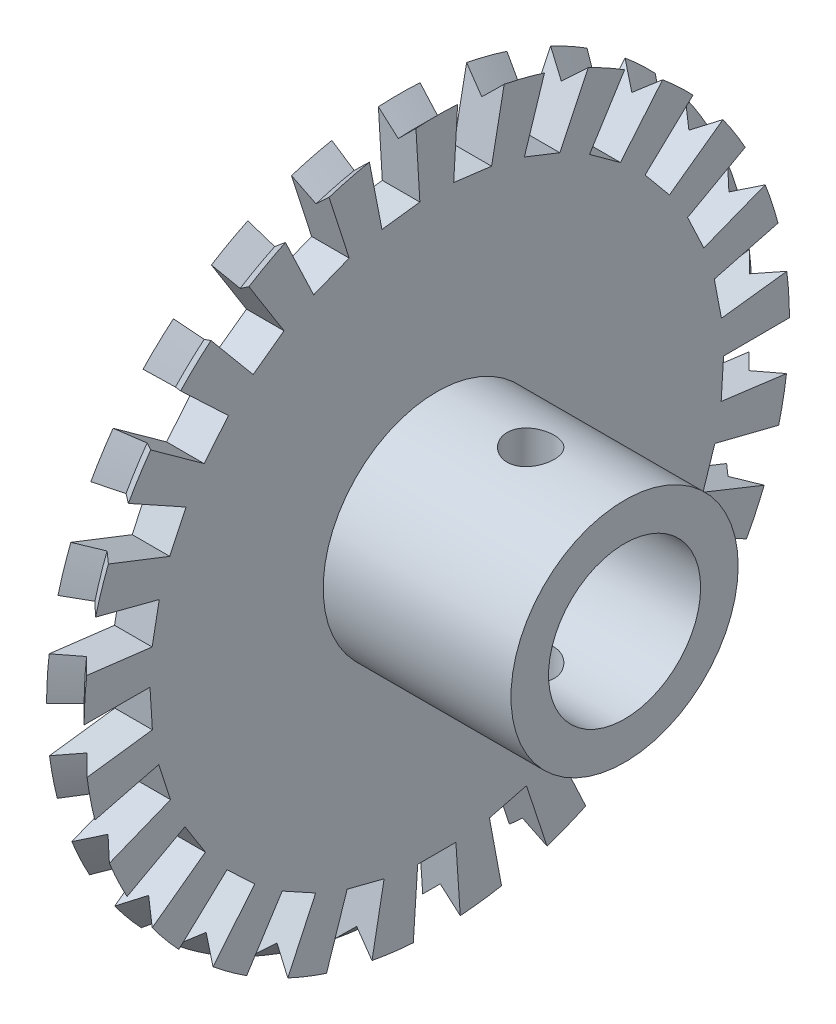
SolidWorks part; units mm, degrees
ref_plane "Front Plane" through (0, 0, 0) normal (0, 0, 1) x (1, 0, 0)
ref_plane "Top Plane" through (0, 0, 0) normal (0, 1, 0) x (1, 0, 0)
ref_plane "Right Plane" through (0, 0, 0) normal (1, 0, 0) x (0, 0, -1)
sketch "Sketch2" plane through (0, 0, 0) normal (1, 0, 0) x (0, 0, -1)
  circle A0 centre (0, 0) radius 20.28 construction
  circle A1 centre (0, 0) radius 4.05
  circle A2 centre (0, 0) radius 17.78 construction
  circle A3 centre (0, 0) radius 18.78
  dimension "D1" = 8.1
  dimension "D2" = 40.56
  dimension "D3" = 1
  dimension "D4" = 2.5
extrude "Boss-Extrude1" add sketch "Sketch2" along normal mid plane 2
sketch "Sketch9" plane through (1, 0, 0) normal (1, 0, 0) x (0, 0, -1)
  circle A0 centre (0, 0) radius 6.05
  circle A1 centre (0, 0) radius 4.05
  circle A2 centre (0, 0) radius 4.05 construction
  dimension "D1" = 2
extrude "Boss-Extrude2" add sketch "Sketch9" along normal blind 10
sketch "Sketch5" plane through (0, 0, 0) normal (0, 1, 0) x (1, 0, 0)
  line L0 (-1, -18.78) -> (0, -17.78)
  line L1 (0, -17.78) -> (1, -18.78)
  line L2 (-1, -18.78) -> (1, -18.78) construction
  line L3 (-1, -18.78) -> (1, -18.78)
  dimension "D1" = 1
ref_axis "Axis1" through (11, 0, 0) along (-1, 0, 0)
revolve "Cut-Revolve1" cut sketch "Sketch5" angle 360 about axis through (11, 0, 0) along (-1, 0, 0)
sketch "Sketch7" plane through (-1, 0, 0) normal (-1, 0, 0) x (0, 0, 1)
  circle A0 centre (0, 0) radius 17.78 construction
  circle A1 centre (0, 0) radius 20.28 construction
  dimension "D1" = 40.56
  dimension "D2" = 2.5
sketch "Sketch10" plane through (0, 0, 0) normal (0, 1, 0) x (1, 0, 0)
  line L0 (11, -6.05) -> (11, 6.05) construction
  line L1 (11, 0) -> (-1, 0) construction
  circle A0 centre (6, 0) radius 1.25
  dimension "D1" = 2.5
  dimension "D2" = 5
extrude "Cut-Extrude1" cut sketch "Sketch10" against normal mid plane 20
sketch "Sketch12" plane through (1, 0, 0) normal (1, 0, 0) x (0, 0, -1)
  line L0 (-0.0128, 0.1926) -> (1.3661, -20.4794) construction
  line L1 (-0.0001, -0.0014) -> (-1.4003, -20.9917) construction
  line L2 (1.25, -18.7384) -> (-1.25, -18.7384) construction
  line L3 (1.25, -18.7384) -> (1.0165, -15.2384)
  line L4 (1.0165, -15.2384) -> (-1.0165, -15.2384)
  line L5 (-1.0165, -15.2384) -> (-1.25, -18.7384)
  circle A0 centre (0, 0) radius 18.78 construction
  arc A1 (1.25, 18.7384) -> (1.25, -18.7384) centre (0, 0) ccw
  circle M5 centre (0, 0) radius 18.78
  dimension "D1" = 2.5
  dimension "D2" = 3.5
extrude "Cut-Extrude3" cut sketch "Sketch12" against normal mid plane 20 contours L4 L5 L3 M5
pattern_circular "CirPattern1" count 25 over 360 about axis through (0, 0, 0) along (1, 0, 0) of "Cut-Extrude3"
